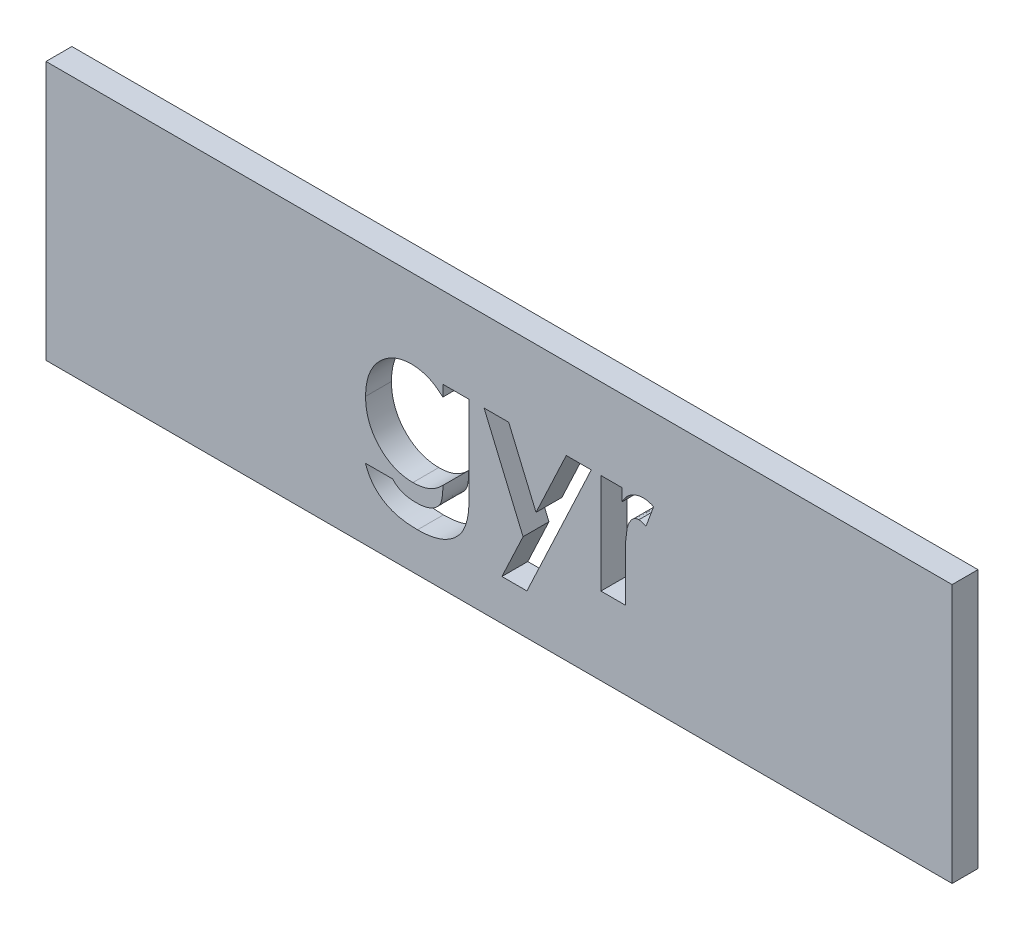
SolidWorks part; units mm, degrees
ref_plane "Plan de face" through (0, 0, 0) normal (0, 0, 1) x (1, 0, 0)
ref_plane "Plan de dessus" through (0, 0, 0) normal (0, 1, 0) x (1, 0, 0)
ref_plane "Plan de droite" through (0, 0, 0) normal (1, 0, 0) x (0, 0, -1)
sketch "Esquisse1" plane through (0, 0, 0) normal (0, 0, 1) x (1, 0, 0)
  line L1 (0, 0) -> (35, 0)
  line L2 (0, 0) -> (0, -10)
  line L3 (0, -10) -> (35, -10)
  line L4 (35, 0) -> (35, -10)
  dimension "D1" = 35
  dimension "D2" = 10
extrude "Boss.-Extru.1" add sketch "Esquisse1" along normal blind 1
sketch "Esquisse2" plane through (0, 0, 0) normal (0, 0, -1) x (-1, 0, 0)
  line L0 (-35, 0) -> (0, 0) construction
  line L1 (-35, -10) -> (-35, 0) construction
  line L2 (0, 0) -> (0, -10) construction
  circle A0 centre (-30, -5) radius 1
  circle A1 centre (-5, -5) radius 1
  dimension "D4" = 2
  dimension "D1" = 5
  dimension "D2" = 5
  dimension "D3" = 5
extrude "Boss.-Extru.2" add sketch "Esquisse2" along normal blind 3
chamfer "Chanfrein1" distance 0.5 angle 45 2 edges at (29, -5, -3) (4, -5, -3)
sketch "Esquisse3" plane through (0, 0, 1) normal (0, 0, 1) x (1, 0, 0)
  line L0 (7.5, -7) -> (27.5, -7) construction
  line L3 (0, -10) -> (35, -10) construction
  line L4 (0, 0) -> (0, -10) construction
  line L5 (35, -10) -> (35, 0) construction
  text T1 "<b>gyr</b>" font "Century Gothic" height in points 20
  point P12 (27.5, -7)
  dimension "D1" = 3
  dimension "D2" = 7.5
  dimension "D3" = 20
  dimension "D4" = 7.5
extrude "Enlèv. mat.-Extru.2" cut sketch "Esquisse3" against normal blind 1
